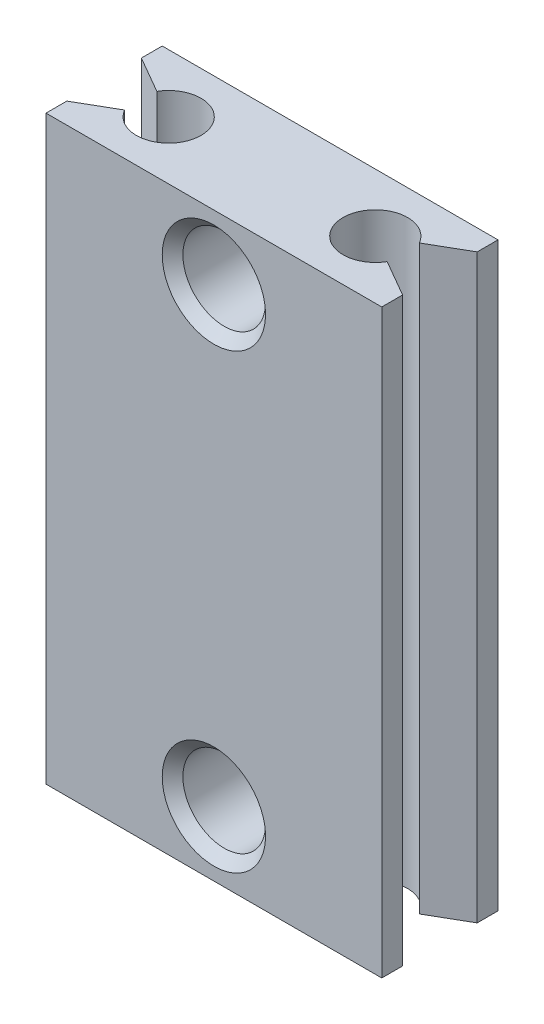
SolidWorks part; units mm, degrees
material "6061 Alloy"
ref_plane "Front Plane" through (0, 0, 0) normal (0, 0, 1) x (1, 0, 0)
ref_plane "Top Plane" through (0, 0, 0) normal (0, 1, 0) x (1, 0, 0)
ref_plane "Right Plane" through (0, 0, 0) normal (1, 0, 0) x (0, 0, -1)
sketch "Base Sketch" plane through (0, 0, 0) normal (0, 1, 0) x (1, 0, 0)
  line L1 (-6.5, -4.5) -> (6.5, -4.5)
  line L2 (-6.5, -4.5) -> (-6.5, 0)
  line L3 (-6.5, 0) -> (6.5, 0)
  line L4 (6.5, -4.5) -> (6.5, 0)
  point P4 (0, 0)
  dimension "D1" = 13
  dimension "D2" = 4.5
extrude "Block Size" add sketch "Base Sketch" along normal blind 22.5
hole_wizard "M3 Clearance Hole1" positions "Sketch2" profile "Sketch3" hole size "M3" standard "ANSI Metric" end condition through all
sketch "Sketch2" plane through (0, 0, 0) normal (0, 0, 1) x (1, 0, 0)
  line L0 (0, -2.475) -> (0, 2.475) construction
  line L1 (2.475, 0) -> (-2.475, 0) construction
  line L2 (6.5, 22.5) -> (-6.5, 22.5) construction
  circle A0 centre (0, 2.5) radius 2 construction
  circle A1 centre (0, 20) radius 2 construction
  point P0 (0, 20)
  point P2 (0, 2.5)
  dimension "D1" = 4
  dimension "D2" = 0.5
  dimension "D3" = 0.5
sketch "Sketch3" plane through (0, 20, 0) normal (1, 0, 0) x (0, 1, 0)
  line L0 (0, 0) -> (0, 4.5)
  line L1 (0, 4.5) -> (2, 4.5)
  line L2 (1.6, 4.1) -> (1.6, 0.4)
  line L3 (1.6, 0.4) -> (2, 0)
  line L5 (2, 0) -> (0, 0)
  line L6 (-1.6, 0.4) -> (-2, 0) construction
  line L7 (2, 4.5) -> (1.6, 4.1)
  line L8 (-2, 4.5) -> (-1.6, 4.1) construction
  line L11 (0, -6.35) -> (0, 107.95) construction
  dimension "Thru Hole Dia." = 3.2
  dimension "Thru Hole Depth" = 4.5
  dimension "Near C'Sink Dia." = 4
  dimension "Near C'Sink Angle" = 90
  dimension "Far C'Sink Dia." = 4
  dimension "Far C'Sink Angle" = 90
hole_wizard "M3x0.5 Tapped Hole1" positions "Sketch4" profile "Sketch5" tap size "M3x0.5" standard "ANSI Metric" end condition through all
sketch "Sketch4" plane through (0, 0, 0) normal (0, 1, 0) x (1, 0, 0)
  line L0 (-6.5, -4.5) -> (-6.5, 0) construction
  line L4 (-4, -2.25) -> (4, -2.25) construction
  line L6 (0, -2.475) -> (0, 2.475) construction
  circle A0 centre (-4, -2.25) radius 1.25 construction
  circle A1 centre (4, -2.25) radius 1.25 construction
  point P0 (-4, -2.25)
  point P2 (4, -2.25)
  point P8 (-6.5, -2.25)
  point P23 (0, -2.25)
  dimension "D1" = 2.5
  dimension "D2" = 2.5
sketch "Sketch5" plane through (-4, 0, 2.25) normal (1, 0, 0) x (0, 0, -1)
  line L0 (0, 0) -> (0, 22.5)
  line L1 (0, 22.5) -> (1.25, 22.5)
  line L2 (1.25, 22.5) -> (1.25, 0)
  line L5 (1.25, 0) -> (0, 0)
  line L11 (0, -6.35) -> (0, 107.95) construction
  dimension "Thru Tap Drill Dia." = 2.5
  dimension "Thru Tap Drill Depth" = 22.5
cosmetic thread "Hole Thread1" parameters "D2"=3
cosmetic thread "Hole Thread2" parameters "D2"=3
sketch "Sketch6" plane through (0, 0, 0) normal (0, 1, 0) x (1, 0, 0)
  line L0 (-6.5, -0.8066) -> (-4, -2.25)
  line L1 (-4, -2.25) -> (-6.5, -3.6934)
  line L2 (-6.5, -3.6934) -> (-6.5, -0.8066)
  line L3 (4, -2.25) -> (6.5, -0.8066)
  line L4 (6.5, -0.8066) -> (6.5, -3.6934)
  line L5 (6.5, -3.6934) -> (4, -2.25)
  line L7 (-6.5, -4.5) -> (-6.5, 0) construction
extrude "Side Cuts" cut sketch "Sketch6" along normal through all
